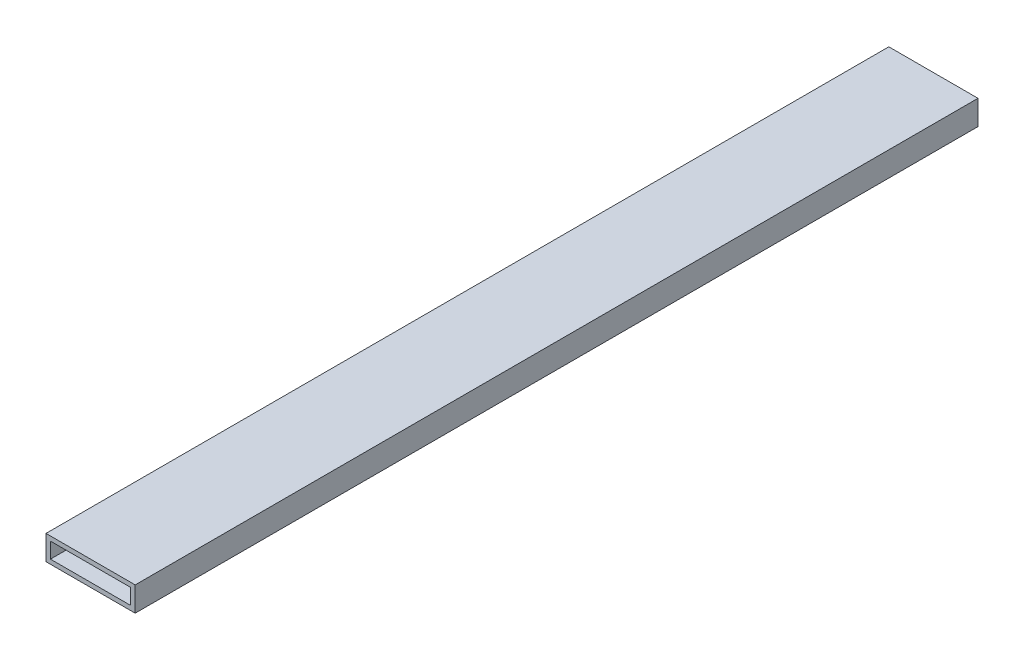
SolidWorks part; units mm, degrees
ref_plane "Front Plane" through (0, 0, 0) normal (0, 0, 1) x (1, 0, 0)
ref_plane "Top Plane" through (0, 0, 0) normal (0, 1, 0) x (1, 0, 0)
ref_plane "Right Plane" through (0, 0, 0) normal (1, 0, 0) x (0, 0, -1)
sketch "Sketch1" plane through (0, 0, 0) normal (0, 0, 1) x (1, 0, 0)
  line L0 (-18, 3.5) -> (18, 3.5)
  line L1 (-20, -5.5) -> (20, -5.5)
  line L2 (-20, -5.5) -> (-20, 5.5)
  line L3 (-20, 5.5) -> (20, 5.5)
  line L4 (20, -5.5) -> (20, 5.5)
  line L5 (-20, -5.5) -> (20, 5.5) construction
  line L6 (-20, 5.5) -> (20, -5.5) construction
  line L7 (18, -3.5) -> (18, 3.5)
  line L8 (-18, -3.5) -> (18, -3.5)
  line L9 (-18, -3.5) -> (-18, 3.5)
  point P0 (0, 0)
  dimension "D1" = 11
  dimension "D2" = 40
  dimension "D3" = 2
extrude "Boss-Extrude1" add sketch "Sketch1" along normal blind 378
